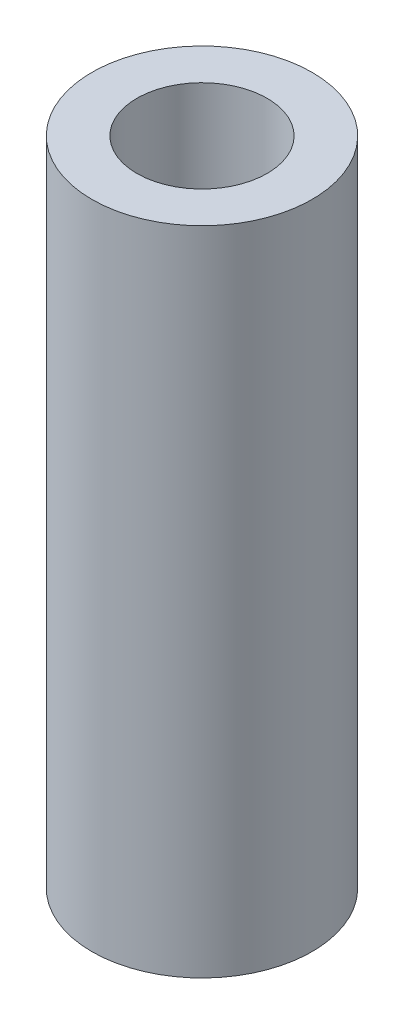
SolidWorks part; units mm, degrees
ref_plane "Front Plane" through (0, 0, 0) normal (0, 0, 1) x (1, 0, 0)
ref_plane "Top Plane" through (0, 0, 0) normal (0, 1, 0) x (1, 0, 0)
ref_plane "Right Plane" through (0, 0, 0) normal (1, 0, 0) x (0, 0, -1)
sketch "Sketch1" plane through (0, 0, 0) normal (0, 1, 0) x (1, 0, 0)
  circle A0 centre (0, 0) radius 6.35
  circle A1 centre (0, 0) radius 10.7315
  dimension "D1" = 12.7
  dimension "D2" = 21.463
extrude "Boss-Extrude1" add sketch "Sketch1" along normal mid plane 63.5 contours A1 | A0
